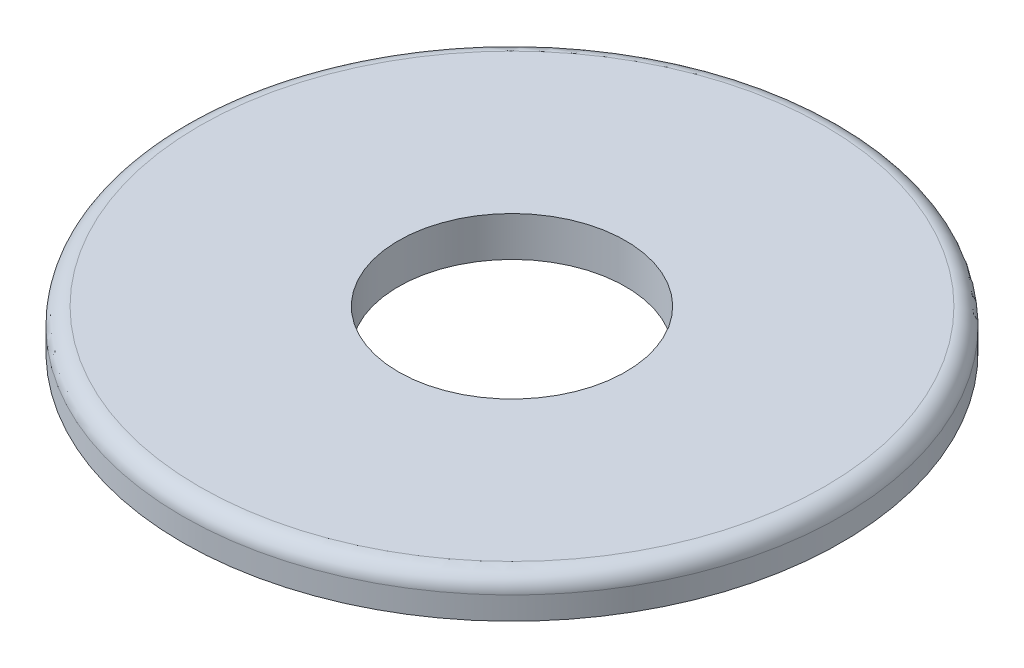
SolidWorks part; units mm, degrees
ref_plane "Front Plane" through (0, 0, 0) normal (0, 0, 1) x (1, 0, 0)
ref_plane "Top Plane" through (0, 0, 0) normal (0, 1, 0) x (1, 0, 0)
ref_plane "Right Plane" through (0, 0, 0) normal (1, 0, 0) x (0, 0, -1)
sketch "Sketch1" plane through (0, 0, 0) normal (0, 1, 0) x (1, 0, 0)
  circle A0 centre (0, 0) radius 184.15
  circle A1 centre (0, 0) radius 63.5
  dimension "D1" = 368.3
extrude "Boss-Extrude1" add sketch "Sketch1" along normal blind 22.225
fillet "Fillet1" radius 9.525 1 edges at (0, 22.225, 184.15)
sketch "Sketch2" plane through (0, 0, 0) normal (0, 1, 0) x (1, 0, 0)
  line L0 (0, 0) -> (-174.625, 0) construction
  line L2 (-85.4446, -57.15) -> (-161.6446, -57.15)
  line L3 (-85.4446, -57.15) -> (-85.4446, 57.15)
  line L4 (-85.4446, 57.15) -> (-161.6446, 57.15)
  line L5 (-161.6446, -57.15) -> (-161.6446, 57.15)
  line L6 (-85.4446, -57.15) -> (-161.6446, 57.15) construction
  line L7 (-85.4446, 57.15) -> (-161.6446, -57.15) construction
  circle A0 centre (0, 0) radius 174.625 construction
  circle A1 centre (0, 0) radius 174.625 construction
  circle A2 centre (0, 0) radius 171.45 construction
  dimension "D1" = 76.2
  dimension "D2" = 114.3
  dimension "D3" = 3.175
extrude "Cut-Extrude4" [suppressed] cut sketch "Sketch2" along normal through all
